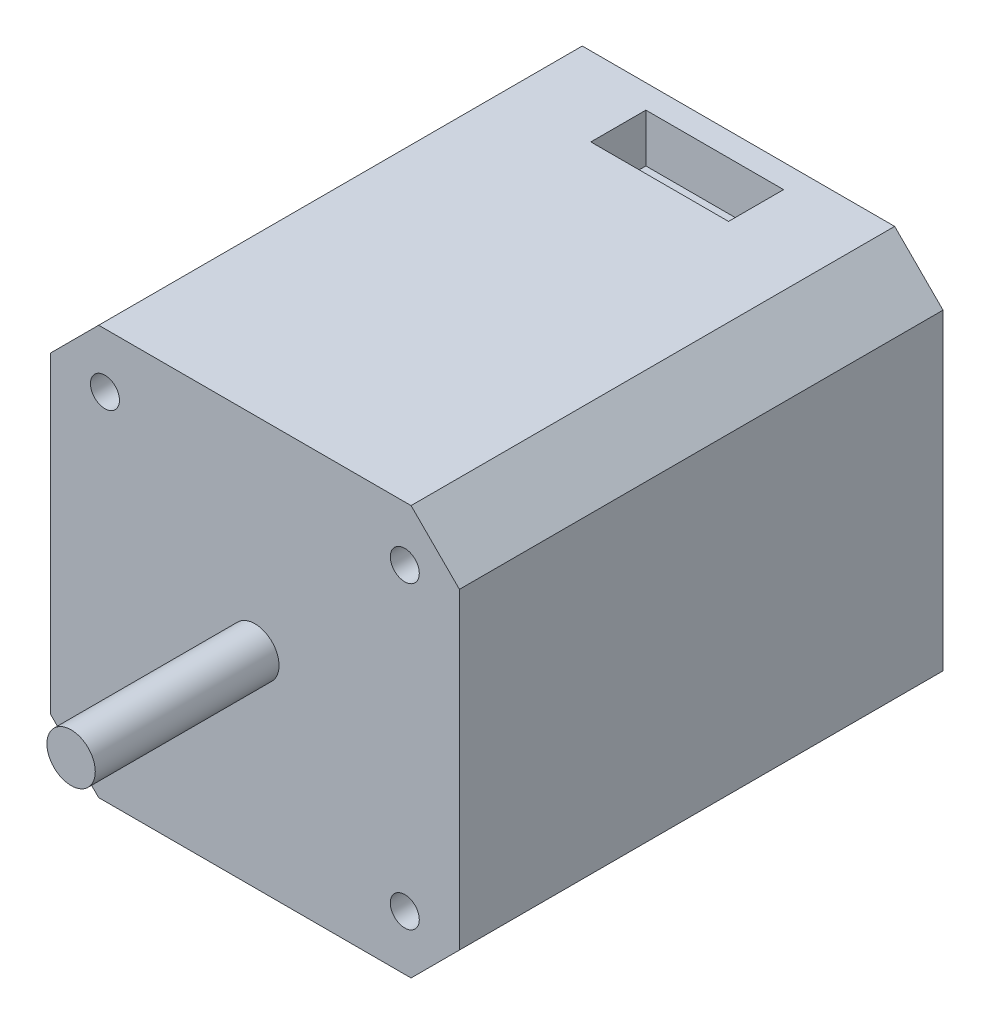
SolidWorks part; units mm, degrees
material "Vanadium"
ref_plane "Front Plane" through (0, 0, 0) normal (0, 0, 1) x (1, 0, 0)
ref_plane "Top Plane" through (0, 0, 0) normal (0, 1, 0) x (1, 0, 0)
ref_plane "Right Plane" through (0, 0, 0) normal (1, 0, 0) x (0, 0, -1)
sketch "Sketch1" plane through (0, 0, 0) normal (0, 0, 1) x (1, 0, 0)
  line L0 (-16.15, 21.15) -> (-21.15, 16.15)
  line L1 (-16.15, 21.15) -> (16.15, 21.15)
  line L2 (-21.15, 16.15) -> (-21.15, -16.15)
  line L3 (-16.15, -21.15) -> (16.15, -21.15)
  line L4 (21.15, 16.15) -> (21.15, -16.15)
  line L5 (-21.15, 21.15) -> (21.15, -21.15) construction
  line L6 (-21.15, -21.15) -> (21.15, 21.15) construction
  line L7 (16.15, 21.15) -> (21.15, 16.15)
  line L8 (21.15, -16.15) -> (16.15, -21.15)
  line L9 (-21.15, -16.15) -> (-16.15, -21.15)
  point P0 (0, 0)
  dimension "D1" = 42.3
  dimension "D2" = 42.3
extrude "Boss-Extrude1" add sketch "Sketch1" along normal blind 50
sketch "Sketch2" plane through (0, 0, 50) normal (0, 0, 1) x (1, 0, 0)
  circle A0 centre (0, 0) radius 2.5
extrude "Boss-Extrude2" add sketch "Sketch2" along normal blind 24
sketch "Sketch3" plane through (0, 0, 50) normal (0, 0, 1) x (1, 0, 0)
  circle A0 centre (-15.5, 15.5) radius 1.5
  circle A1 centre (-15.5, -15.5) radius 1.5
  circle A2 centre (15.5, -15.5) radius 1.5
  circle A3 centre (15.5, 15.5) radius 1.5
  point P0 (0, 0)
  dimension "D1" = 31
  dimension "D2" = 31
extrude "Cut-Extrude1" cut sketch "Sketch3" against normal blind 24
sketch "Sketch4" plane through (0, 21.15, 0) normal (0, 1, 0) x (1, 0, 0)
  line L1 (-7.1179, -8.1464) -> (7.1179, -8.1464)
  line L2 (-7.1179, -8.1464) -> (-7.1179, -2.4521)
  line L3 (-7.1179, -2.4521) -> (7.1179, -2.4521)
  line L4 (7.1179, -8.1464) -> (7.1179, -2.4521)
  line L5 (-7.1179, -8.1464) -> (7.1179, -2.4521) construction
  line L6 (-7.1179, -2.4521) -> (7.1179, -8.1464) construction
  point P0 (0, -5.2992)
extrude "Cut-Extrude2" cut sketch "Sketch4" against normal blind 5
sketch "Sketch5" plane through (0, 0, 50) normal (0, 0, 1) x (1, 0, 0)
  line L1 (-21.15, 0) -> (21.15, 0) construction
  line L3 (-21.15, 16.15) -> (-21.15, -16.15) construction
  line L4 (21.15, -16.15) -> (21.15, 16.15) construction
  line L5 (-15.5, -15.5) -> (-15.5, -21.15) construction
  line L6 (-16.15, -21.15) -> (16.15, -21.15) construction
  dimension "D1" = 42.3
  dimension "D2" = 5.65
sketch "Sketch6" plane through (0, 0, 74) normal (0, 0, 1) x (1, 0, 0)
  circle A0 centre (0, 0) radius 2.5
extrude "Cut-Extrude3" cut sketch "Sketch6" against normal blind 5
